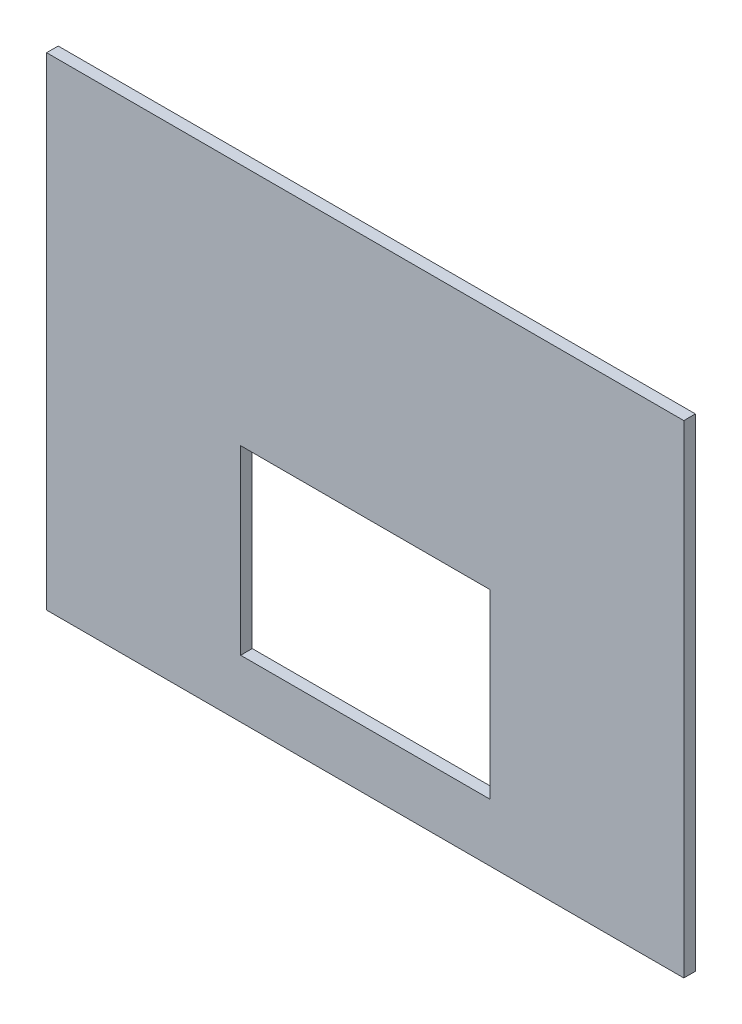
SolidWorks part; units mm, degrees
ref_plane "Plan de face" through (0, 0, 0) normal (0, 0, 1) x (1, 0, 0)
ref_plane "Plan de dessus" through (0, 0, 0) normal (0, 1, 0) x (1, 0, 0)
ref_plane "Plan de droite" through (0, 0, 0) normal (1, 0, 0) x (0, 0, -1)
sketch "Esquisse1" plane through (0, 0, 0) normal (0, 0, 1) x (1, 0, 0)
  line L1 (-129.2363, 197.8999) -> (200.7637, 197.8999)
  line L2 (-129.2363, 197.8999) -> (-129.2363, -52.1001)
  line L3 (-129.2363, -52.1001) -> (200.7637, -52.1001)
  line L4 (200.7637, 197.8999) -> (200.7637, -52.1001)
  line L5 (-28.7363, 71.8999) -> (100.2637, 71.8999)
  line L6 (-28.7363, 71.8999) -> (-28.7363, -22.1001)
  line L7 (-28.7363, -22.1001) -> (100.2637, -22.1001)
  line L8 (100.2637, 71.8999) -> (100.2637, -22.1001)
  dimension "D1" = 330
  dimension "D2" = 250
  dimension "D3" = 94
  dimension "D4" = 129
  dimension "D5" = 30
  dimension "D6" = 100.5
  dimension "D7" = 100.5
extrude "Boss.-Extru.1" add sketch "Esquisse1" along normal blind 6
